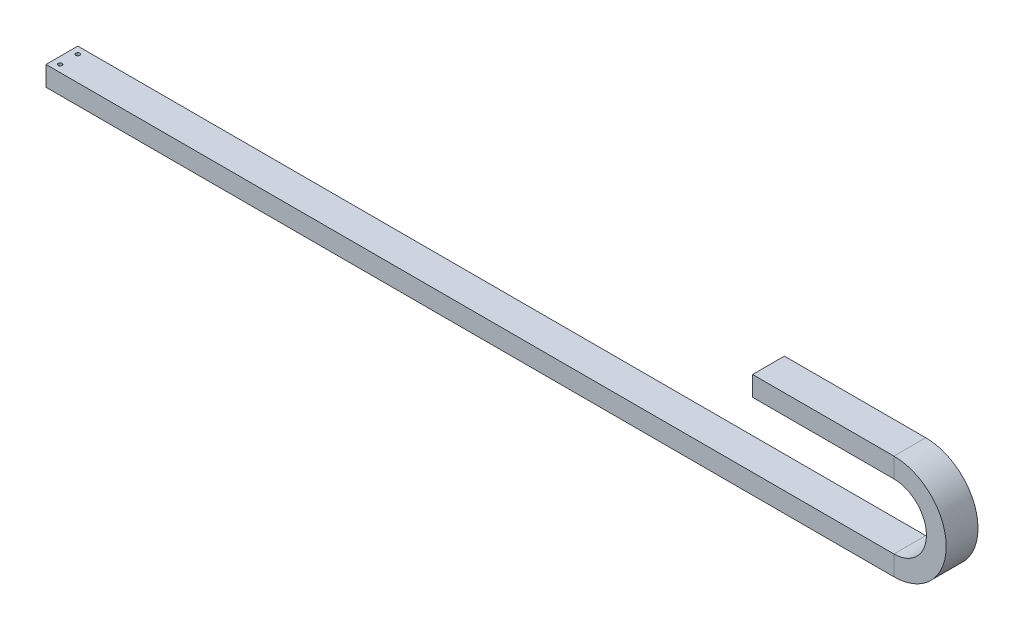
SolidWorks part; units mm, degrees
material "A3钢"
ref_plane "前视基准面" through (0, 0, 0) normal (0, 0, 1) x (1, 0, 0)
ref_plane "上视基准面" through (0, 0, 0) normal (0, 1, 0) x (1, 0, 0)
ref_plane "右视基准面" through (0, 0, 0) normal (1, 0, 0) x (0, 0, -1)
sketch "草图1" plane through (0, 0, 0) normal (0, 0, 1) x (1, 0, 0)
  line L0 (0, 0) -> (1200, 0)
  line L1 (1200, 120) -> (1000, 120)
  arc A0 (1200, 0) -> (1200, 120) centre (1200, 60) ccw
  dimension "D1" = 60
  dimension "D2" = 1200
  dimension "D3" = 200
sketch "草图2" plane through (0, 0, 0) normal (1, 0, 0) x (0, 0, -1)
  line L1 (-22.5, -14) -> (22.5, -14)
  line L2 (-22.5, -14) -> (-22.5, 14)
  line L3 (-22.5, 14) -> (22.5, 14)
  line L4 (22.5, -14) -> (22.5, 14)
  line L5 (-22.5, -14) -> (22.5, 14) construction
  line L6 (-22.5, 14) -> (22.5, -14) construction
  line L7 (17.5, -9) -> (-17.5, -9)
  line L8 (17.5, -9) -> (17.5, 9)
  line L9 (17.5, 9) -> (-17.5, 9)
  line L10 (-17.5, -9) -> (-17.5, 9)
  line L11 (17.5, -9) -> (-17.5, 9) construction
  line L12 (17.5, 9) -> (-17.5, -9) construction
  point P0 (0, 0)
  point P5 (0, 0)
  dimension "D1" = 28
  dimension "D2" = 45
  dimension "D3" = 5
  dimension "D4" = 5
sweep "扫描1" add profiles "草图2" path "草图1"
sketch "草图3" plane through (0, 14, 0) normal (0, 1, 0) x (1, 0, 0)
  line L0 (0, 0) -> (89.8522, 0) construction
  line L1 (0, 22.5) -> (0, -22.5) construction
  line L2 (10, -12.5) -> (10, 12.5) construction
  point P6 (0, 0)
  dimension "D1" = 10
  dimension "D2" = 25
hole_wizard "Ø5.5 (5.5) 直径孔1" positions "3D草图1" profile "草图4" hole size "Ø5.5" standard "GB" end condition through all
sketch3d "3D草图1"
  point P2 (10, 14, -12.5)
  point P4 (10, 14, 12.5)
  point P7 (0, 0, 0)
  point P9 (0, 0, 0)
sketch "草图4" plane through (10, 14, -12.5) normal (1, 0, 0) x (0, 0, 1)
  line L0 (0, 0) -> (0, 28)
  line L1 (0, 28) -> (2.75, 28)
  line L2 (2.75, 28) -> (2.75, 0)
  line L5 (2.75, 0) -> (0, 0)
  line L11 (0, -6.35) -> (0, 107.95) construction
  dimension "通孔孔直径" = 5.5
  dimension "通孔孔深度" = 28
